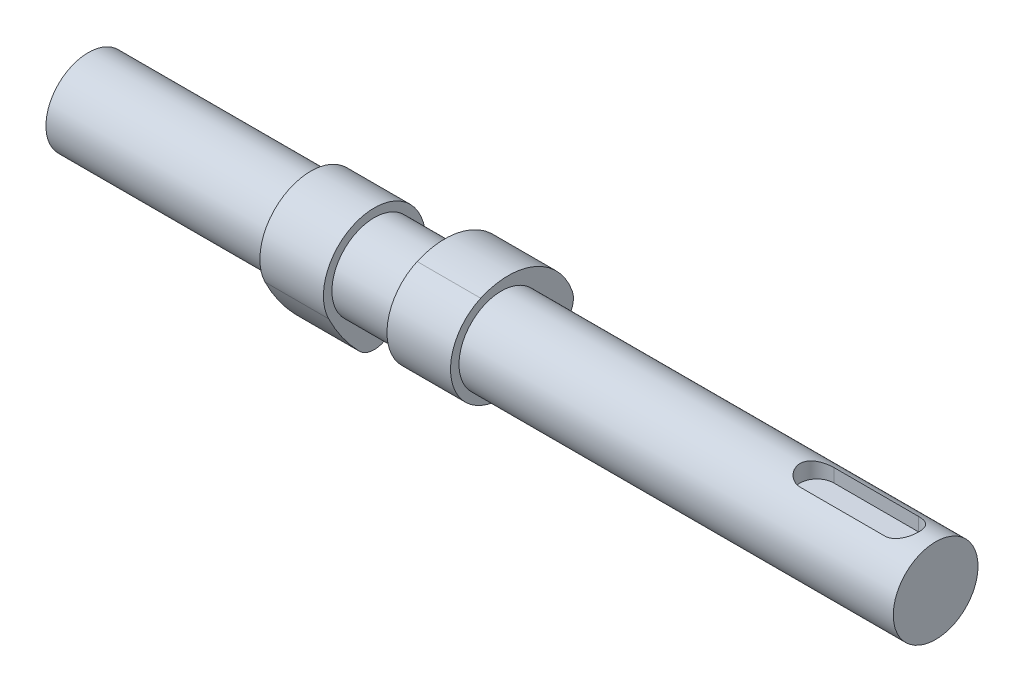
SolidWorks part; units mm, degrees
ref_plane "Front Plane" through (0, 0, 0) normal (0, 0, 1) x (1, 0, 0)
ref_plane "Top Plane" through (0, 0, 0) normal (0, 1, 0) x (1, 0, 0)
ref_plane "Right Plane" through (0, 0, 0) normal (1, 0, 0) x (0, 0, -1)
sketch "Sketch1" plane through (0, 0, 0) normal (1, 0, 0) x (0, 0, -1)
  circle A0 centre (0, 0) radius 10
  dimension "D1" = 20
extrude "Boss-Extrude1" add sketch "Sketch1" against normal blind 75 and the other way blind 125
sketch "Sketch2" plane through (0, 0, 0) normal (1, 0, 0) x (0, 0, -1)
  line L0 (0, 0) -> (7, 0) construction
  arc A0 (-4.875, 10.9651) -> (5.3036, -10.7644) centre (0, 0) ccw
  arc A1 (15.4821, -3.5881) -> (16.7159, 1.6614) centre (12, 0) ccw
  arc A2 (-4.875, 10.9651) -> (16.7159, 1.6614) centre (1.625, -3.655) cw
  arc A3 (5.3036, -10.7644) -> (15.4821, -3.5881) centre (-12.375, 25.1169) ccw
  dimension "D1" = 24
  dimension "D2" = 10
  dimension "D3" = 16
  dimension "D4" = 40
extrude "Boss-Extrude2" add sketch "Sketch2" along normal mid plane 15 from offset 15 separate body
mirror "Mirror3" about plane through (0, 0, 0) normal (1, 0, 0) of bodies 102
move or copy body "Body-Move/Copy2" bodies to move or copy 103 copy no rotation origin (0, 0, 0) rotation axis (-1, 0, 0) rotation angle 90
ref_plane "Plane1" through (0, 10, 0) normal (0, 1, 0) x (1, 0, 0)
sketch "Sketch3" plane through (0, 10, 0) normal (0, 1, 0) x (1, 0, 0)
  line L0 (125, 0) -> (56.6002, 0) construction
  line L1 (125, -10) -> (125, 10) construction
  line L2 (117, 0) -> (97, 0) construction
  line L3 (117, -4) -> (97, -4)
  line L4 (117, 4) -> (97, 4)
  arc A0 (117, -4) -> (117, 4) centre (117, 0) ccw
  arc A1 (97, 4) -> (97, -4) centre (97, 0) ccw
  point P7 (107, 0)
  dimension "D3" = 4
  dimension "D1" = 20
  dimension "D2" = 8
extrude "Cut-Extrude1" cut sketch "Sketch3" against normal blind 4
